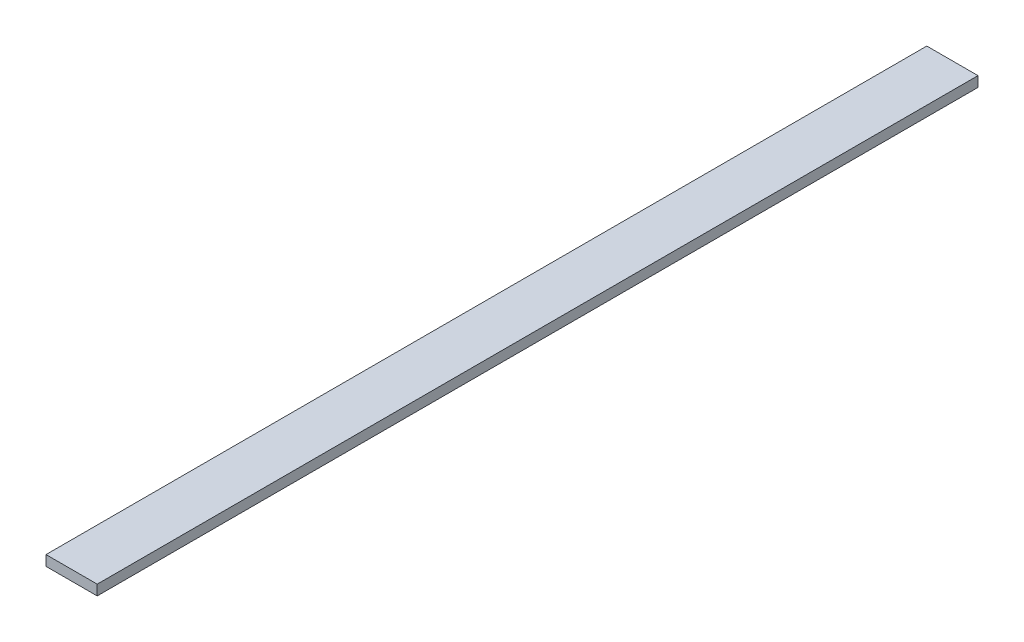
SolidWorks part; units mm, degrees
ref_plane "Front Plane" through (0, 0, 0) normal (0, 0, 1) x (1, 0, 0)
ref_plane "Top Plane" through (0, 0, 0) normal (0, 1, 0) x (1, 0, 0)
ref_plane "Right Plane" through (0, 0, 0) normal (1, 0, 0) x (0, 0, -1)
sketch "Sketch1" plane through (0, 0, 0) normal (0, 1, 0) x (1, 0, 0)
  line L0 (0, 0) -> (50, 0)
  line L1 (50, 0) -> (50, 860)
  line L2 (50, 860) -> (0, 860)
  line L3 (0, 860) -> (0, 0)
  dimension "D1" = 50
  dimension "D2" = 860
extrude "Boss-Extrude1" add sketch "Sketch1" along normal blind 10
